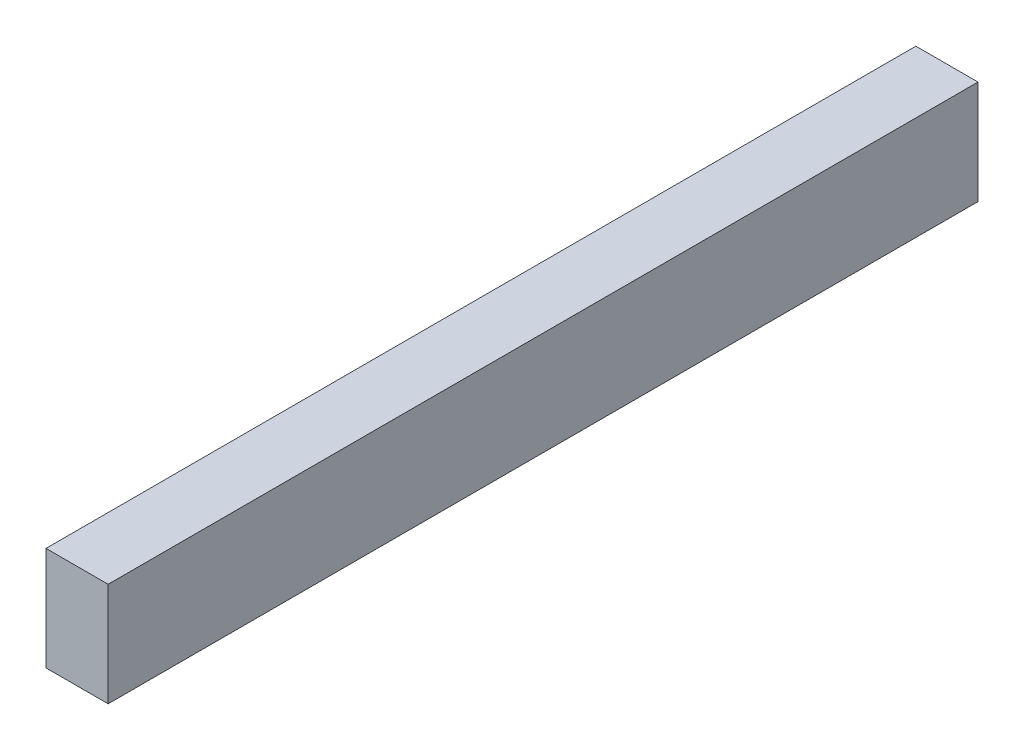
SolidWorks part; units mm, degrees
ref_plane "Front Plane" through (0, 0, 0) normal (0, 0, 1) x (1, 0, 0)
ref_plane "Top Plane" through (0, 0, 0) normal (0, 1, 0) x (1, 0, 0)
ref_plane "Right Plane" through (0, 0, 0) normal (1, 0, 0) x (0, 0, -1)
sketch "Sketch1" plane through (0, 0, 0) normal (0, 0, 1) x (1, 0, 0)
  line L1 (-19.05, -31.75) -> (19.05, -31.75)
  line L2 (-19.05, -31.75) -> (-19.05, 31.75)
  line L3 (-19.05, 31.75) -> (19.05, 31.75)
  line L4 (19.05, -31.75) -> (19.05, 31.75)
  line L5 (-19.05, -31.75) -> (19.05, 31.75) construction
  line L6 (-19.05, 31.75) -> (19.05, -31.75) construction
  point P0 (0, 0)
  dimension "D1" = 63.5
  dimension "D2" = 38.1
extrude "Boss-Extrude1" add sketch "Sketch1" along normal blind 533.4
